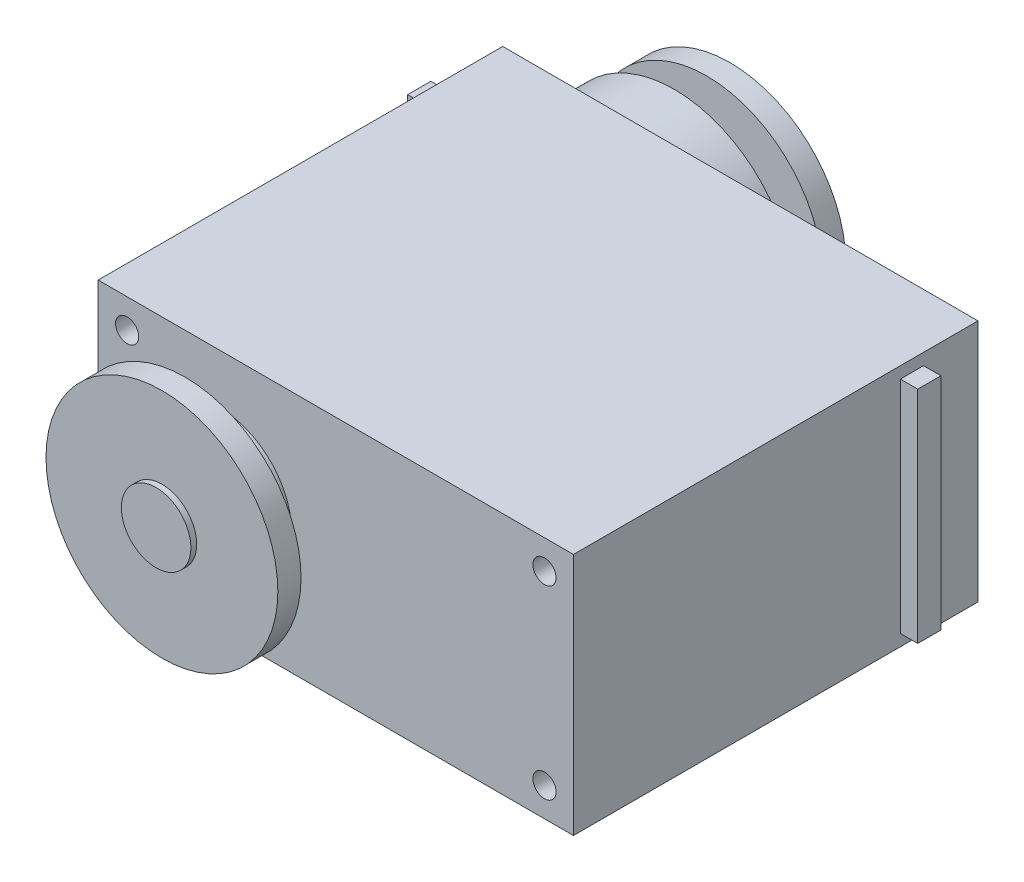
SolidWorks part; units mm, degrees
ref_plane "前基準面" through (0, 0, 0) normal (0, 0, 1) x (1, 0, 0)
ref_plane "上基準面" through (0, 0, 0) normal (0, 1, 0) x (1, 0, 0)
ref_plane "右基準面" through (0, 0, 0) normal (1, 0, 0) x (0, 0, -1)
sketch "草圖1" plane through (0, 0, 0) normal (0, 0, 1) x (1, 0, 0)
  line L1 (-20.5, 10.5) -> (20.5, 10.5)
  line L2 (-20.5, 10.5) -> (-20.5, -10.5)
  line L3 (-20.5, -10.5) -> (20.5, -10.5)
  line L4 (20.5, 10.5) -> (20.5, -10.5)
  line L5 (-20.5, 10.5) -> (20.5, -10.5) construction
  line L6 (-20.5, -10.5) -> (20.5, 10.5) construction
  point P0 (0, 0)
  point P5 (0, 0)
  dimension "D1" = 41
  dimension "D2" = 21
extrude "填料-伸長1" add sketch "草圖1" along normal blind 34.9
sketch "草圖2" plane through (0, 0, 0) normal (0, 0, -1) x (-1, 0, 0)
  line L0 (20.5, 0) -> (-20.5, 0) construction
  line L1 (20.5, 10.5) -> (20.5, -10.5) construction
  line L2 (-20.5, -10.5) -> (-20.5, 10.5) construction
  line L3 (0, -10.5) -> (0, 10.5) construction
  line L4 (20.5, -10.5) -> (-20.5, -10.5) construction
  line L5 (-20.5, 10.5) -> (20.5, 10.5) construction
  circle A0 centre (10, 0) radius 10.4
  circle A1 centre (-1.2, 0) radius 5.9
  dimension "D2" = 20.8
  dimension "D3" = 11.8
  dimension "D1" = 10
  dimension "D4" = 1.2
extrude "填料-伸長2" add sketch "草圖2" along normal blind 4.3 contours A1 A0 | A0 A1 | A0 A1
sketch "草圖3" plane through (0, 0, -4.3) normal (0, 0, -1) x (-1, 0, 0)
  circle A0 centre (10, 0) radius 5.75
  arc A1 (1.1254, -5.4224) -> (1.1254, 5.4224) centre (10, 0) ccw construction
  dimension "D1" = 11.5
extrude "填料-伸長3" add sketch "草圖3" along normal blind 1.2
sketch "草圖4" plane through (0, 0, -5.5) normal (0, 0, -1) x (-1, 0, 0)
  circle A0 centre (10, 0) radius 3
  circle A1 centre (10, 0) radius 5.75 construction
  dimension "D1" = 6
extrude "填料-伸長4" add sketch "草圖4" along normal blind 3.4
sketch "草圖5" plane through (-20.5, 0, 0) normal (-1, 0, 0) x (0, 0, 1)
  line L0 (34.9, 10.5) -> (34.9, -10.5) construction
  line L1 (4.7, -9.5) -> (6.7, -9.5)
  line L2 (4.7, -9.5) -> (4.7, 9.5)
  line L3 (4.7, 9.5) -> (6.7, 9.5)
  line L4 (6.7, -9.5) -> (6.7, 9.5)
  line L5 (0, 0) -> (34.9, 0) construction
  line L6 (0, 10.5) -> (0, -10.5) construction
  point P10 (4.7, 0)
  dimension "D1" = 2
  dimension "D2" = 28.2
  dimension "D3" = 19
extrude "填料-伸長5" add sketch "草圖5" along normal blind 1.5
mirror "鏡射1" about plane through (0, 0, 0) normal (1, 0, 0) of "填料-伸長5"
sketch "草圖6" plane through (0, 0, 34.9) normal (0, 0, 1) x (1, 0, 0)
  line L0 (-20.5, 0) -> (20.5, 0) construction
  line L1 (-20.5, 10.5) -> (-20.5, -10.5) construction
  line L2 (20.5, -10.5) -> (20.5, 10.5) construction
  line L3 (0, 10.5) -> (0, -10.5) construction
  line L4 (20.5, 10.5) -> (-20.5, 10.5) construction
  line L5 (-20.5, -10.5) -> (20.5, -10.5) construction
  circle A0 centre (-10, 0) radius 6.2
  dimension "D2" = 12.4
  dimension "D1" = 10
extrude "填料-伸長6" add sketch "草圖6" along normal blind 2
sketch "草圖7" plane through (0, 0, 36.9) normal (0, 0, 1) x (1, 0, 0)
  circle A0 centre (-10, 0) radius 3
  circle A1 centre (-10, 0) radius 6.2 construction
  dimension "D1" = 6
extrude "填料-伸長7" add sketch "草圖7" along normal blind 3.5
sketch "草圖8" plane through (0, 0, 34.9) normal (0, 0, 1) x (1, 0, 0)
  line L0 (-20.5, 0) -> (20.5, 0) construction
  line L1 (-20.5, 10.5) -> (-20.5, -10.5) construction
  line L2 (20.5, -10.5) -> (20.5, 10.5) construction
  line L3 (0, 10.5) -> (0, -10.5) construction
  line L4 (20.5, 10.5) -> (-20.5, 10.5) construction
  line L5 (-20.5, -10.5) -> (20.5, -10.5) construction
  circle A0 centre (-18, 8) radius 1
  circle A1 centre (18, 8) radius 1
  circle A2 centre (18, -8) radius 1
  circle A3 centre (-18, -8) radius 1
  dimension "D1" = 18
  dimension "D3" = 2
  dimension "D2" = 8
extrude "除料-伸長1" cut sketch "草圖8" against normal blind 10
sketch "草圖9" plane through (0, 0, 36.9) normal (0, 0, 1) x (1, 0, 0)
  circle A0 centre (-10, 0) radius 5
  circle A1 centre (-10, 0) radius 6.2 construction
  dimension "D1" = 10
extrude "填料-伸長8" add sketch "草圖9" along normal blind 1
sketch "草圖10" plane through (0, 0, 37.9) normal (0, 0, 1) x (1, 0, 0)
  circle A0 centre (-10, 0) radius 10
  dimension "D1" = 20
extrude "填料-伸長9" add sketch "草圖10" along normal blind 2
sketch "草圖11" plane through (0, 0, -5.5) normal (0, 0, -1) x (-1, 0, 0)
  circle A0 centre (10, 0) radius 5
  dimension "D1" = 10
extrude "填料-伸長10" add sketch "草圖11" along normal blind 1.6
sketch "草圖12" plane through (0, 0, -7.1) normal (0, 0, -1) x (-1, 0, 0)
  circle A0 centre (10, 0) radius 10
  dimension "D1" = 20
extrude "填料-伸長11" add sketch "草圖12" along normal blind 2
